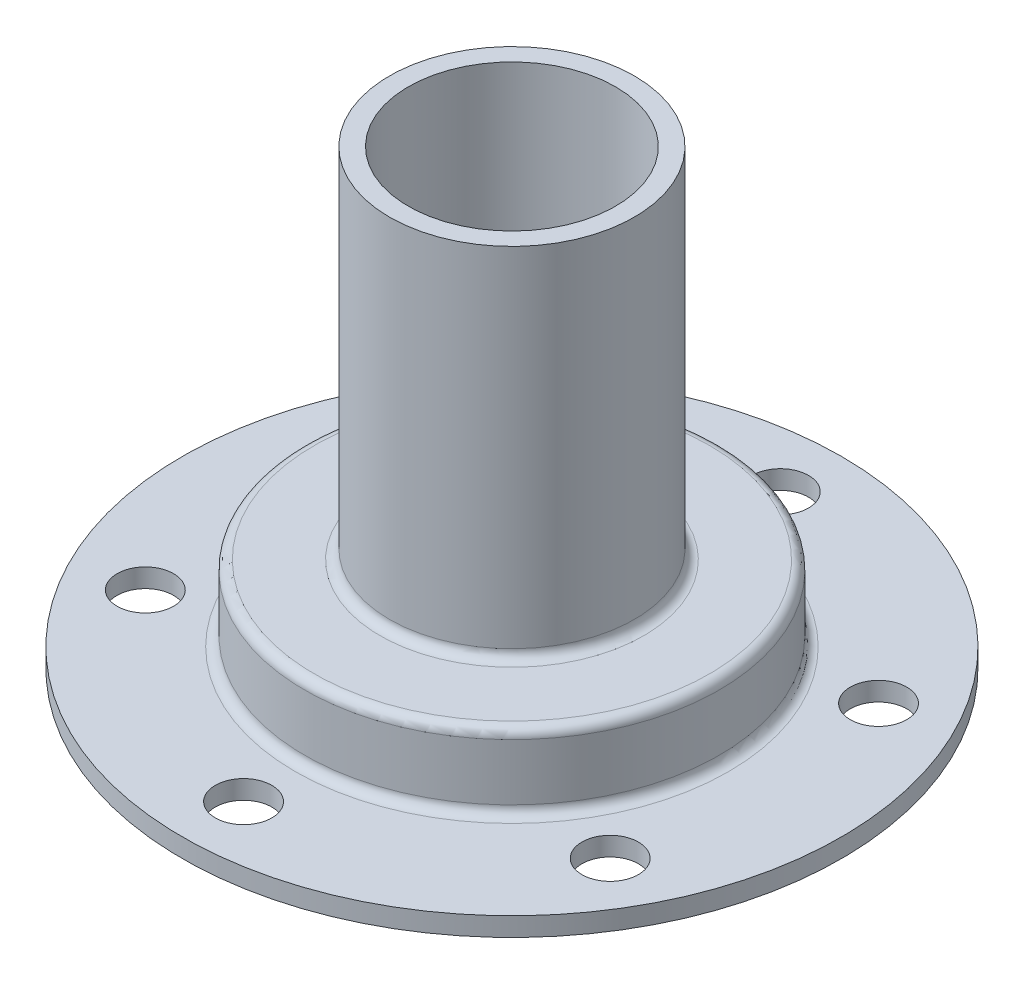
SolidWorks part; units mm, degrees
material "普通碳钢"
ref_plane "前视基准面" through (0, 0, 0) normal (0, 0, 1) x (1, 0, 0)
ref_plane "上视基准面" through (0, 0, 0) normal (0, 1, 0) x (1, 0, 0)
ref_plane "右视基准面" through (0, 0, 0) normal (1, 0, 0) x (0, 0, -1)
sketch "草图1" plane through (0, 0, 0) normal (0, 0, 1) x (1, 0, 0)
  line L0 (0, 0) -> (0, 81.5505) construction
  line L3 (20, 0) -> (35, 0)
  line L4 (35, 0) -> (35, 2)
  line L5 (35, 2) -> (23, 2)
  line L6 (22, 3) -> (22, 9)
  line L7 (21, 10) -> (14, 10)
  line L8 (13, 11) -> (13, 48)
  line L9 (13, 48) -> (11, 48)
  line L10 (11, 48) -> (11, 8)
  line L11 (11, 8) -> (19, 8)
  line L12 (20, 7) -> (20, 0)
  arc A0 (23, 2) -> (22, 3) centre (23, 3) cw
  arc A1 (19, 8) -> (20, 7) centre (19, 7) cw
  arc A2 (22, 9) -> (21, 10) centre (21, 9) ccw
  arc A3 (14, 10) -> (13, 11) centre (14, 11) cw
  dimension "D9" = 1
  dimension "D2" = 2
  dimension "D3" = 2
  dimension "D4" = 2
  dimension "D5" = 13
  dimension "D6" = 2
  dimension "D7" = 40
  dimension "D8" = 10
  dimension "D10" = 20
  dimension "D11" = 35
revolve "旋转1" add sketch "草图1" angle 360 about L0
sketch "草图2" plane through (0, 2, 0) normal (0, 1, 0) x (1, 0, 0)
  circle A0 centre (0, 28.5) radius 3
  circle A1 centre (24.6817, 14.25) radius 3
  circle A2 centre (24.6817, -14.25) radius 3
  circle A3 centre (0, -28.5) radius 3
  circle A4 centre (-24.6817, -14.25) radius 3
  circle A5 centre (-24.6817, 14.25) radius 3
  point P15 (0, 0)
  dimension "D1" = 28.5
  dimension "D3" = 6
  dimension "D2" = 6
extrude "切除-拉伸1" cut sketch "草图2" against normal through all
sketch "草图3" plane through (0, 0, 0) normal (1, 0, 0) x (0, 0, -1)
  circle A0 centre (0, 31.336) radius 2.5
extrude "切除-拉伸2" cut sketch "草图3" against normal through all
equation "\"32。5\"=55"
